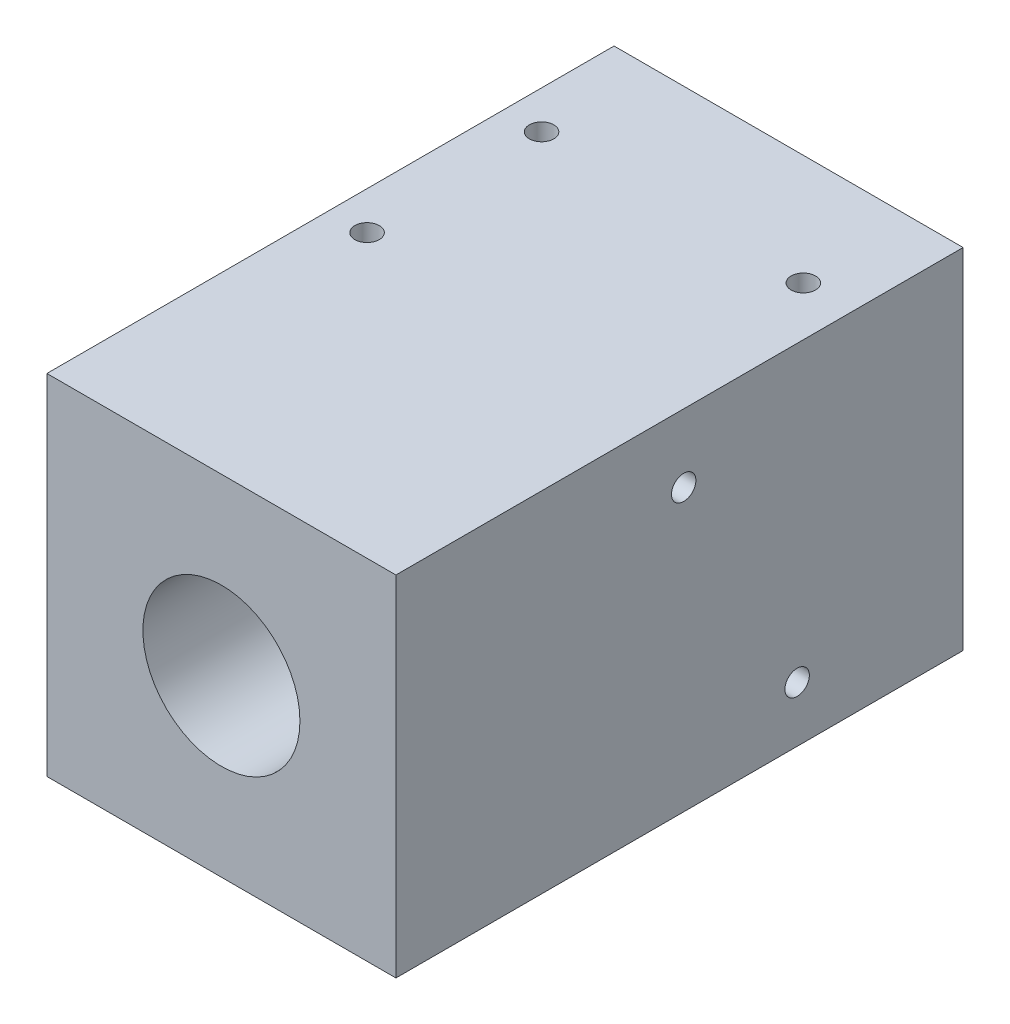
SolidWorks part; units mm, degrees
ref_plane "Front Plane" through (0, 0, 0) normal (0, 0, 1) x (1, 0, 0)
ref_plane "Top Plane" through (0, 0, 0) normal (0, 1, 0) x (1, 0, 0)
ref_plane "Right Plane" through (0, 0, 0) normal (1, 0, 0) x (0, 0, -1)
sketch "Sketch1" plane through (0, 0, 0) normal (0, 0, 1) x (1, 0, 0)
  line L1 (-20, -20) -> (20, -20)
  line L2 (-20, -20) -> (-20, 20)
  line L3 (-20, 20) -> (20, 20)
  line L4 (20, -20) -> (20, 20)
  line L5 (-20, -20) -> (20, 20) construction
  line L6 (-20, 20) -> (20, -20) construction
  circle A0 centre (0, 0) radius 9
  point P0 (0, 0)
  dimension "D2" = 18
  dimension "D1" = 40
extrude "Boss-Extrude1" add sketch "Sketch1" along normal blind 65
sketch "Sketch2" plane through (0, 20, 0) normal (0, 1, 0) x (1, 0, 0)
  line L0 (-20.0634, -0.1729) -> (19.9366, -0.1729) construction
  circle A0 centre (14.3648, -12.6729) radius 1.4
  circle A1 centre (-15.6352, -32.6729) radius 1.4
  circle A2 centre (-15.6352, -12.6729) radius 1.4
extrude "Cut-Extrude1" cut sketch "Sketch2" against normal through all contours A2 | A1 | A0
sketch "Sketch3" plane through (20, 0, 0) normal (1, 0, 0) x (0, 0, -1)
  line L0 (-0.0212, 20.1215) -> (-0.0212, -19.8785) construction
  circle A0 centre (-19.0212, -13.6413) radius 1.4
  circle A1 centre (-32.0212, 12.2053) radius 1.4
extrude "Cut-Extrude2" cut sketch "Sketch3" against normal blind 65 contours A1 | A0
